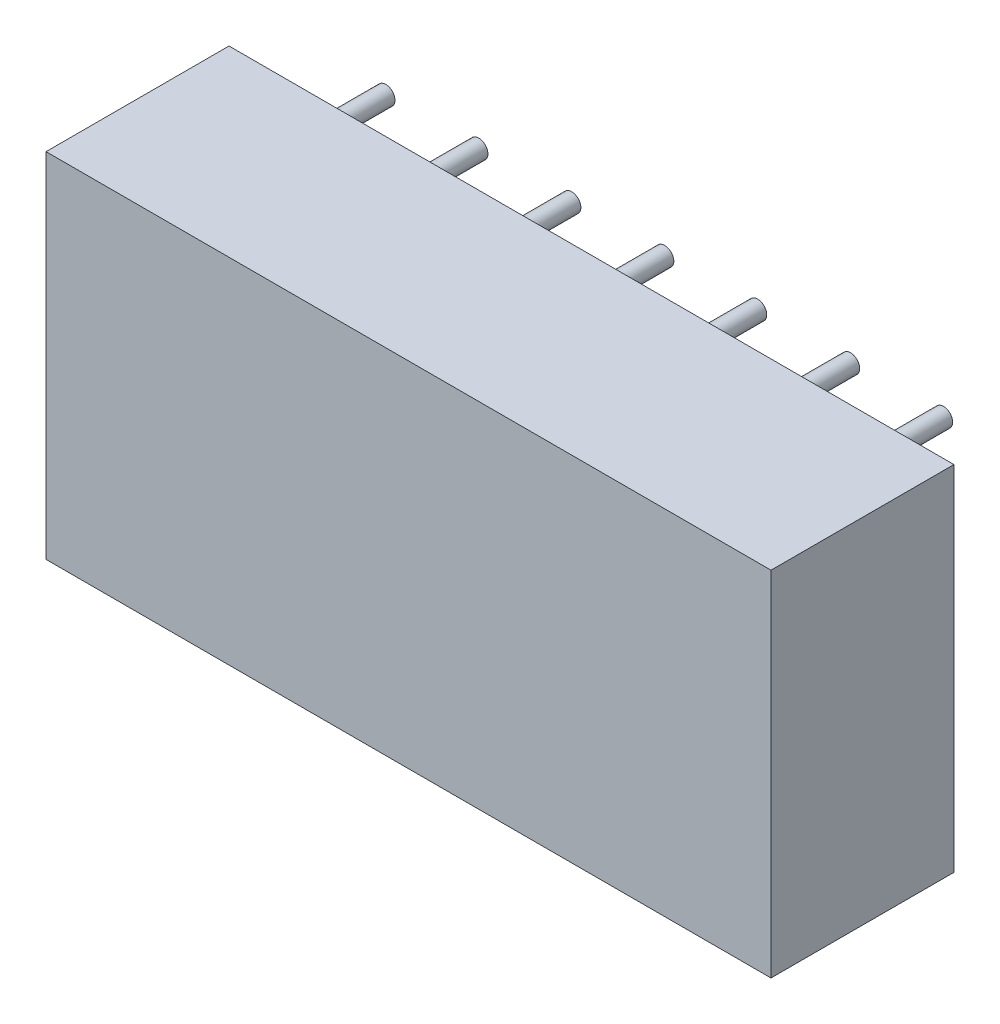
SolidWorks part; units mm, degrees
ref_plane "Front Plane" through (0, 0, 0) normal (0, 0, 1) x (1, 0, 0)
ref_plane "Top Plane" through (0, 0, 0) normal (0, 1, 0) x (1, 0, 0)
ref_plane "Right Plane" through (0, 0, 0) normal (1, 0, 0) x (0, 0, -1)
sketch "Sketch1" plane through (0, 0, 0) normal (0, 0, 1) x (1, 0, 0)
  line L0 (-2.286, 8.636) -> (-2.286, -1.016)
  line L1 (-2.286, -1.016) -> (17.526, -1.016)
  line L2 (17.526, -1.016) -> (17.526, 8.636)
  line L3 (17.526, 8.636) -> (-2.286, 8.636)
extrude "Component_Outline" add sketch "Sketch1" along normal blind 5 separate body
sketch "Sketch2" plane through (0, 0, 0) normal (0, 0, 1) x (1, 0, 0)
  circle A0 centre (0, 0) radius 0.25
extrude "1" add sketch "Sketch2" against normal blind 2 separate body
sketch "Sketch3" plane through (0, 0, 0) normal (0, 0, 1) x (1, 0, 0)
  circle A0 centre (2.54, 0) radius 0.25
extrude "2" add sketch "Sketch3" against normal blind 2 separate body
sketch "Sketch4" plane through (0, 0, 0) normal (0, 0, 1) x (1, 0, 0)
  circle A0 centre (5.08, 0) radius 0.25
extrude "3" add sketch "Sketch4" against normal blind 2 separate body
sketch "Sketch5" plane through (0, 0, 0) normal (0, 0, 1) x (1, 0, 0)
  circle A0 centre (7.62, 0) radius 0.25
extrude "4" add sketch "Sketch5" against normal blind 2 separate body
sketch "Sketch6" plane through (0, 0, 0) normal (0, 0, 1) x (1, 0, 0)
  circle A0 centre (10.16, 0) radius 0.25
extrude "5" add sketch "Sketch6" against normal blind 2 separate body
sketch "Sketch7" plane through (0, 0, 0) normal (0, 0, 1) x (1, 0, 0)
  circle A0 centre (12.7, 0) radius 0.25
extrude "6" add sketch "Sketch7" against normal blind 2 separate body
sketch "Sketch8" plane through (0, 0, 0) normal (0, 0, 1) x (1, 0, 0)
  circle A0 centre (15.24, 0) radius 0.25
extrude "7" add sketch "Sketch8" against normal blind 2 separate body
sketch "Sketch9" plane through (0, 0, 0) normal (0, 0, 1) x (1, 0, 0)
  circle A0 centre (15.24, 7.62) radius 0.25
extrude "8" add sketch "Sketch9" against normal blind 2 separate body
sketch "Sketch10" plane through (0, 0, 0) normal (0, 0, 1) x (1, 0, 0)
  circle A0 centre (12.7, 7.62) radius 0.25
extrude "9" add sketch "Sketch10" against normal blind 2 separate body
sketch "Sketch11" plane through (0, 0, 0) normal (0, 0, 1) x (1, 0, 0)
  circle A0 centre (10.16, 7.62) radius 0.25
extrude "10" add sketch "Sketch11" against normal blind 2 separate body
sketch "Sketch12" plane through (0, 0, 0) normal (0, 0, 1) x (1, 0, 0)
  circle A0 centre (7.62, 7.62) radius 0.25
extrude "11" add sketch "Sketch12" against normal blind 2 separate body
sketch "Sketch13" plane through (0, 0, 0) normal (0, 0, 1) x (1, 0, 0)
  circle A0 centre (5.08, 7.62) radius 0.25
extrude "12" add sketch "Sketch13" against normal blind 2 separate body
sketch "Sketch14" plane through (0, 0, 0) normal (0, 0, 1) x (1, 0, 0)
  circle A0 centre (2.54, 7.62) radius 0.25
extrude "13" add sketch "Sketch14" against normal blind 2 separate body
sketch "Sketch15" plane through (0, 0, 0) normal (0, 0, 1) x (1, 0, 0)
  circle A0 centre (0, 7.62) radius 0.25
extrude "14" add sketch "Sketch15" against normal blind 2 separate body
sketch3d "3DSketch1"
  line L0 (0, 0, 0) -> (1, 0, 0)
  line L1 (0, 0, 0) -> (0, 1, 0)
  line L2 (0, 0, 0) -> (0, 0, 1)
  point P0 (0, 0, 0)
